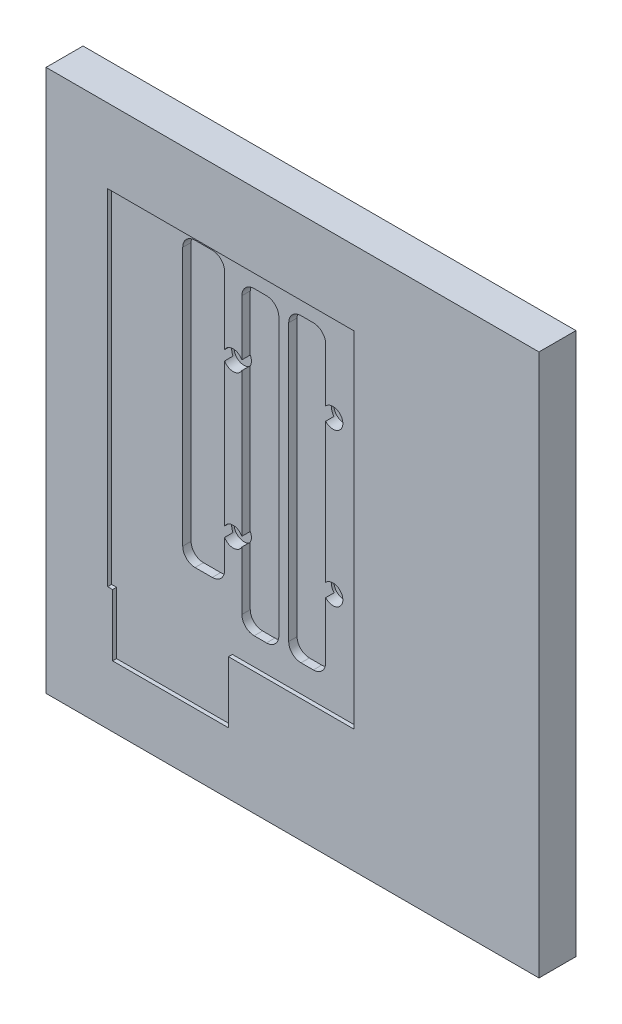
SolidWorks part; units mm, degrees
ref_plane "Plan de face" through (0, 0, 0) normal (0, 0, 1) x (1, 0, 0)
ref_plane "Plan de dessus" through (0, 0, 0) normal (0, 1, 0) x (1, 0, 0)
ref_plane "Plan de droite" through (0, 0, 0) normal (1, 0, 0) x (0, 0, -1)
sketch "Esquisse1" plane through (0, 0, 0) normal (0, 0, 1) x (1, 0, 0)
  line L1 (0, 0) -> (200, 0)
  line L2 (0, 0) -> (0, 220)
  line L3 (0, 220) -> (200, 220)
  line L4 (200, 0) -> (200, 220)
  dimension "D1" = 220
  dimension "D2" = 200
extrude "Boss.-Extru.1" add sketch "Esquisse1" along normal blind 15 contours L2 L3 L4 L1
sketch "Esquisse2" plane through (0, 0, 15) normal (0, 0, 1) x (1, 0, 0)
  line L0 (-18.9017, 50) -> (217.441, 50) construction
  line L1 (25, -8.0253) -> (25, 235.7005) construction
  line L2 (0, 0) -> (0, 220) construction
  line L4 (0, 0) -> (200, 0) construction
  circle A0 centre (74.322, 91.45) radius 4
  circle A1 centre (74.322, 153.45) radius 4
  circle A2 centre (114.822, 91.45) radius 4
  circle A3 centre (114.822, 153.45) radius 4
  dimension "D3" = 49.322
  dimension "D4" = 41.45
  dimension "D5" = 62
  dimension "D6" = 40.5
  dimension "D7" = 62
  dimension "D1" = 25
  dimension "D2" = 50
  dimension "D8" = 40.5
  dimension "D9" = 41.45
extrude "Enlèv. mat.-Extru.1" cut sketch "Esquisse2" against normal blind 6
sketch "Esquisse3" plane through (0, 0, 15) normal (0, 0, 1) x (1, 0, 0)
  line L0 (25, -28.7793) -> (25, 217.9356) construction
  line L1 (-8.7891, 50) -> (218.6275, 50) construction
  line L2 (0, 0) -> (0, 220) construction
  line L3 (0, 0) -> (200, 0) construction
  line L4 (27, 50) -> (27, 24.9288)
  line L6 (25, 50) -> (25, 189.8757)
  line L7 (25, 189.8757) -> (124.85, 189.8757)
  line L8 (124.85, 49.9157) -> (124.85, 189.8757)
  line L9 (27, 24.9288) -> (74, 24.9288)
  line L10 (74, 24.9288) -> (74, 49.9157)
  line L11 (74, 49.9157) -> (124.85, 49.9157)
  line L12 (25, 50) -> (27, 50)
  dimension "D1" = 25
  dimension "D2" = 50
  dimension "D3" = 99.85
  dimension "D4" = 139.96
  dimension "D5" = 2
  dimension "D6" = 47
extrude "Enlèv. mat.-Extru.2" cut sketch "Esquisse3" against normal blind 1.6
sketch "Esquisse4" plane through (0, 0, 15) normal (0, 0, 1) x (1, 0, 0)
  line L6 (124.85, 49.9157) -> (124.85, 189.8757) construction
  line L11 (106.85, 182.8757) -> (101.85, 182.8757)
  line L12 (111.85, 177.8757) -> (111.85, 65.8757)
  line L13 (106.85, 60.8757) -> (101.85, 60.8757)
  line L14 (96.85, 177.8757) -> (96.85, 65.8757)
  line L15 (87.85, 60.8757) -> (82.85, 60.8757)
  line L16 (92.85, 65.8757) -> (92.85, 177.8757)
  line L17 (87.85, 182.8757) -> (82.85, 182.8757)
  line L18 (77.85, 65.8757) -> (77.85, 177.8757)
  line L19 (65.85, 187.8757) -> (58.85, 187.8757)
  line L20 (70.85, 182.8757) -> (70.85, 77.8757)
  line L21 (65.85, 72.8757) -> (58.85, 72.8757)
  line L22 (53.85, 182.8757) -> (53.85, 77.8757)
  line L23 (124.85, 189.8757) -> (25, 189.8757) construction
  line L24 (124.85, 189.8757) -> (25, 189.8757) construction
  arc A0 (111.85, 65.8757) -> (106.85, 60.8757) centre (106.85, 65.8757) cw
  arc A1 (101.85, 60.8757) -> (96.85, 65.8757) centre (101.85, 65.8757) cw
  arc A2 (87.85, 60.8757) -> (92.85, 65.8757) centre (87.85, 65.8757) ccw
  arc A3 (82.85, 60.8757) -> (77.85, 65.8757) centre (82.85, 65.8757) cw
  arc A4 (70.85, 77.8757) -> (65.85, 72.8757) centre (65.85, 77.8757) cw
  arc A5 (58.85, 72.8757) -> (53.85, 77.8757) centre (58.85, 77.8757) cw
  arc A6 (106.85, 182.8757) -> (111.85, 177.8757) centre (106.85, 177.8757) cw
  arc A7 (101.85, 182.8757) -> (96.85, 177.8757) centre (101.85, 177.8757) ccw
  arc A8 (92.85, 177.8757) -> (87.85, 182.8757) centre (87.85, 177.8757) ccw
  arc A9 (82.85, 182.8757) -> (77.85, 177.8757) centre (82.85, 177.8757) ccw
  arc A10 (65.85, 187.8757) -> (70.85, 182.8757) centre (65.85, 182.8757) cw
  arc A11 (58.85, 187.8757) -> (53.85, 182.8757) centre (58.85, 182.8757) ccw
  point P20 (111.85, 60.8757)
  point P25 (92.85, 60.8757)
  point P32 (53.85, 72.8757)
  point P35 (111.85, 182.8757)
  point P38 (96.85, 182.8757)
  point P41 (92.85, 182.8757)
  point P44 (77.85, 182.8757)
  point P47 (70.85, 187.8757)
  point P50 (53.85, 187.8757)
  dimension "D9" = 7
  dimension "D5" = 5
  dimension "D1" = 13
  dimension "D2" = 15
  dimension "D3" = 15
  dimension "D4" = 4
  dimension "D6" = 7
  dimension "D7" = 2
  dimension "D8" = 7
  dimension "17" = 17
  dimension "D10" = 115
  dimension "D11" = 122
  dimension "D12" = 122
extrude "Enlèv. mat.-Extru.3" cut sketch "Esquisse4" against normal blind 5
